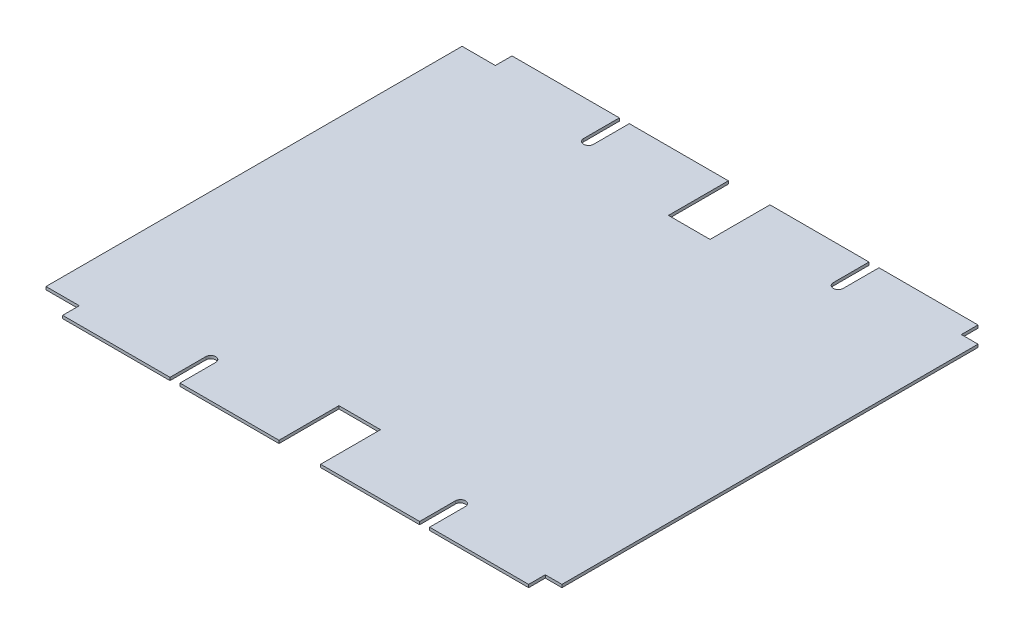
SolidWorks part; units mm, degrees
ref_plane "Front Plane" through (0, 0, 0) normal (0, 0, 1) x (1, 0, 0)
ref_plane "Top Plane" through (0, 0, 0) normal (0, 1, 0) x (1, 0, 0)
ref_plane "Right Plane" through (0, 0, 0) normal (1, 0, 0) x (0, 0, -1)
sketch "Sketch1" plane through (0, 0, 0) normal (0, 1, 0) x (1, 0, 0)
  line L1 (-280, 270) -> (280, 270)
  line L2 (-320, 250) -> (-320, -250)
  line L3 (-280, -270) -> (280, -270)
  line L4 (320, 250) -> (320, -250)
  line L5 (-280, 253.125) -> (280, -253.125) construction
  line L6 (-280, -253.125) -> (280, 253.125) construction
  line L9 (-320, 250) -> (-280, 250)
  line L10 (-280, 270) -> (-280, 250)
  line L13 (320, 250) -> (280, 250)
  line L14 (280, 270) -> (280, 250)
  line L17 (320, -250) -> (280, -250)
  line L18 (280, -270) -> (280, -250)
  line L21 (-320, -250) -> (-280, -250)
  line L22 (-280, -270) -> (-280, -250)
  point P0 (0, 0)
  dimension "D2" = 540
  dimension "D3" = 40
  dimension "D4" = 20
  dimension "D5" = 20
  dimension "D6" = 40
  dimension "D7" = 40
  dimension "D8" = 20
  dimension "D9" = 20
  dimension "D10" = 40
  dimension "D11" = 640
extrude "Boss-Extrude1" add sketch "Sketch1" along normal blind 3.5
sketch "Sketch2" plane through (0, 3.5, 0) normal (0, 1, 0) x (1, 0, 0)
  line L0 (-280, -270) -> (280, -270) construction
  line L2 (30, -250) -> (30, -198)
  line L3 (30, -198) -> (-20, -198)
  line L4 (-20, -250) -> (-20, -198)
  line L5 (-20, 250) -> (30, 198) construction
  line L6 (280, 270) -> (-280, 270) construction
  line L7 (-20, 198) -> (30, 198)
  line L8 (-20, 198) -> (-20, 250)
  line L10 (30, 198) -> (30, 250)
  line L12 (320, -250) -> (320, 250) construction
  line L13 (-20, 250) -> (-20, 270)
  line L14 (320, 250) -> (300, 250)
  line L15 (320, 250) -> (320, 210)
  line L16 (320, 210) -> (300, 210)
  line L17 (300, 250) -> (300, 210)
  line L18 (320, -250) -> (300, -250)
  line L19 (320, -250) -> (320, -210)
  line L20 (320, -210) -> (300, -210)
  line L21 (300, -250) -> (300, -210)
  line L22 (-20, 270) -> (30, 270)
  line L23 (30, 250) -> (30, 270)
  line L25 (-20, -250) -> (-20, -270)
  line L26 (-20, -270) -> (30, -270)
  line L27 (30, -250) -> (30, -270)
  line L28 (30, 250) -> (-20, 198) construction
  point P28 (5, 224)
  point P31 (20.7439, 225.59)
  dimension "D1" = 52
  dimension "D2" = 50
  dimension "D3" = 315
  dimension "D4" = 290
  dimension "D5" = 50
  dimension "D6" = 52
  dimension "D7" = 46
  dimension "D8" = 290
  dimension "D9" = 40
  dimension "D10" = 20
  dimension "D11" = 40
  dimension "D12" = 20
extrude "Cut-Extrude1" cut sketch "Sketch2" against normal blind 10
sketch "Sketch3" plane through (0, 3.5, 0) normal (0, 1, 0) x (1, 0, 0)
  line L0 (300, 250) -> (300, 210) construction
  line L1 (280, 270) -> (30, 270) construction
  line L2 (320, 0) -> (0, 0) construction
  line L4 (149, 227) -> (149, 270)
  line L5 (149, 270) -> (161, 270)
  line L6 (161, 227) -> (161, 270)
  line L7 (320, -210) -> (320, 210) construction
  line L8 (5, 198) -> (5, -198) construction
  line L9 (-20, 198) -> (30, 198) construction
  line L10 (30, -198) -> (-20, -198) construction
  line L11 (161, -227) -> (161, -270)
  line L12 (149, -270) -> (161, -270)
  line L13 (149, -227) -> (149, -270)
  line L14 (-139, -227) -> (-139, -270)
  line L15 (-139, -270) -> (-151, -270)
  line L16 (-151, -227) -> (-151, -270)
  line L17 (-151, 227) -> (-151, 270)
  line L18 (-139, 270) -> (-151, 270)
  line L19 (-139, 227) -> (-139, 270)
  line L20 (-320, 250) -> (-320, -250) construction
  line L21 (-20, 270) -> (-280, 270) construction
  arc A0 (149, 227) -> (161, 227) centre (155, 227) ccw
  arc A1 (149, -227) -> (161, -227) centre (155, -227) cw
  arc A2 (-139, -227) -> (-151, -227) centre (-145, -227) ccw
  arc A3 (-139, 227) -> (-151, 227) centre (-145, 227) cw
  dimension "D1" = 145
  dimension "D2" = 43
  dimension "D3" = 12
  dimension "D4" = 175
  dimension "D5" = 43
extrude "Cut-Extrude2" cut sketch "Sketch3" against normal blind 10
sketch "Sketch4" plane through (0, 3.5, 0) normal (0, 1, 0) x (1, 0, 0)
  line L1 (320, 210) -> (300, 210)
  line L2 (320, 210) -> (320, -210)
  line L3 (320, -210) -> (300, -210)
  line L4 (300, 210) -> (300, -210)
extrude "Cut-Extrude3" cut sketch "Sketch4" against normal through all
